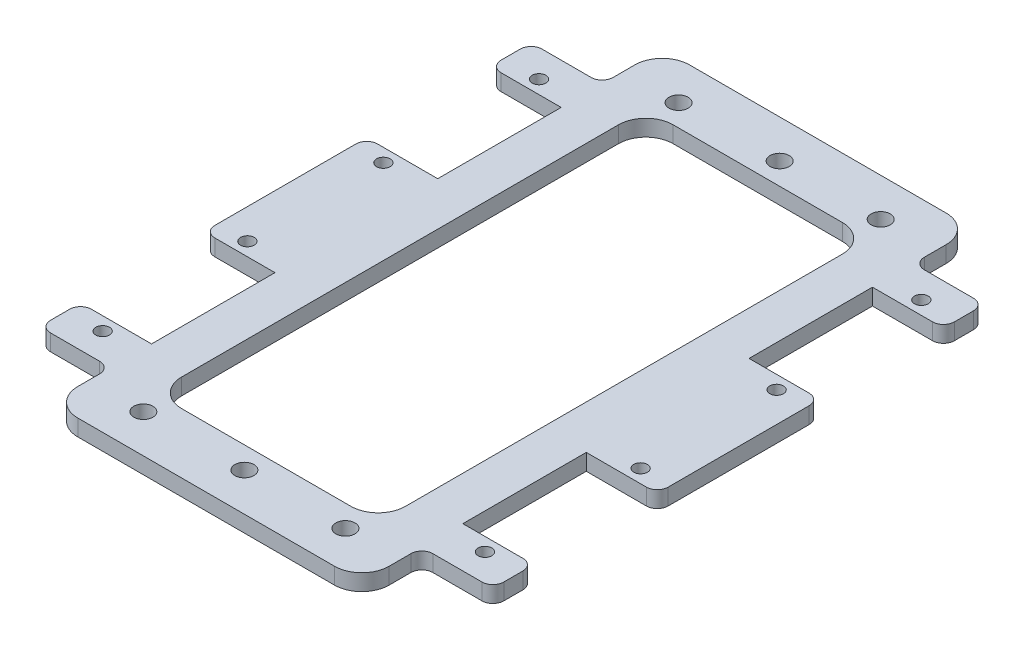
SolidWorks part; units mm, degrees
ref_plane "前视基准面" through (0, 0, 0) normal (0, 0, 1) x (1, 0, 0)
ref_plane "上视基准面" through (0, 0, 0) normal (0, 1, 0) x (1, 0, 0)
ref_plane "右视基准面" through (0, 0, 0) normal (1, 0, 0) x (0, 0, -1)
sketch "草图1" plane through (0, 0, 0) normal (0, 1, 0) x (1, 0, 0)
  line L0 (-41.5, -37.5) -> (-28.5, -37.5)
  line L1 (-28.5, -45) -> (28.5, -45)
  line L2 (-28.5, -45) -> (-28.5, 45)
  line L3 (-28.5, 45) -> (28.5, 45)
  line L4 (28.5, -45) -> (28.5, 45)
  line L5 (-28.5, -45) -> (28.5, 45) construction
  line L6 (-28.5, 45) -> (28.5, -45) construction
  line L7 (-28.5, -45) -> (28.5, -45)
  line L8 (-28.5, -45) -> (-28.5, -56)
  line L9 (-28.5, -56) -> (28.5, -56)
  line L10 (28.5, -45) -> (28.5, -56)
  line L12 (-28.5, 45) -> (-28.5, -45)
  line L13 (-28.5, -45) -> (-41.5, -45)
  line L15 (-41.5, -14.9) -> (-28.5, -14.9)
  line L16 (-41.5, 37.5) -> (-41.5, 45)
  line L17 (-41.5, 37.5) -> (-28.5, 37.5)
  line L18 (-41.5, 14.9) -> (-41.5, -14.9)
  line L19 (-41.5, -37.5) -> (-41.5, -45)
  line L20 (-28.5, 0) -> (-41.5, 0) construction
  line L21 (-41.5, 14.9) -> (-28.5, 14.9)
  line L22 (-28.5, 45) -> (-41.5, 45)
  line L23 (0, 0) -> (0, -45) construction
  line L24 (28.5, 0) -> (41.5, 0) construction
  line L25 (28.5, 45) -> (41.5, 45)
  line L26 (41.5, 14.9) -> (28.5, 14.9)
  line L27 (41.5, -37.5) -> (41.5, -45)
  line L28 (41.5, 14.9) -> (41.5, -14.9)
  line L29 (41.5, 37.5) -> (28.5, 37.5)
  line L30 (41.5, 37.5) -> (41.5, 45)
  line L31 (41.5, -14.9) -> (28.5, -14.9)
  line L32 (28.5, -45) -> (41.5, -45)
  line L33 (41.5, -37.5) -> (28.5, -37.5)
  line L34 (28.5, 45) -> (28.5, 56)
  line L35 (-28.5, 45) -> (-28.5, 56)
  line L36 (-28.5, 56) -> (28.5, 56)
  line L37 (0, -45) -> (0, -53) construction
  line L38 (-20.5, -45) -> (20.5, -45)
  line L39 (-20.5, -45) -> (-20.5, 45)
  line L40 (-20.5, 45) -> (20.5, 45)
  line L41 (20.5, -45) -> (20.5, 45)
  line L42 (-20.5, -45) -> (20.5, 45) construction
  line L43 (-20.5, 45) -> (20.5, -45) construction
  line L44 (0, -53) -> (-4, -53)
  line L45 (0, -53) -> (4, -53)
  line L46 (-4, -53) -> (-4, -45)
  line L47 (4, -53) -> (4, -45)
  line L48 (-4, -45) -> (4, -53) construction
  line L49 (-28.5, -56) -> (-21.871, -56)
  circle A0 centre (-35, -39.95) radius 1.25
  circle A1 centre (-36, -12.45) radius 1.25
  circle A2 centre (-35, 39.95) radius 1.25
  circle A3 centre (-36, 12.45) radius 1.25
  circle A4 centre (36, 12.45) radius 1.25
  circle A5 centre (35, 39.95) radius 1.25
  circle A6 centre (36, -12.45) radius 1.25
  circle A7 centre (35, -39.95) radius 1.25
  circle A8 centre (0, -49) radius 1.75
  circle A9 centre (0, 49) radius 1.75
  circle A10 centre (18.5, -49) radius 1.75
  circle A11 centre (-18.5, -49) radius 1.75
  circle A12 centre (18.5, 49) radius 1.75
  circle A13 centre (-18.5, 49) radius 1.75
  point P0 (0, 0)
  dimension "D9" = 2.5
  dimension "D10" = 2.5
  dimension "D19" = 3.5
  dimension "D1" = 90
  dimension "D2" = 57
  dimension "D3" = 11
  dimension "D4" = 13
  dimension "D5" = 7.5
  dimension "D6" = 22.6
  dimension "D7" = 29.8
  dimension "D8" = 0
  dimension "D11" = 2.45
  dimension "D12" = 2.45
  dimension "D13" = 6.5
  dimension "D14" = 7.5
  dimension "D15" = 8
  dimension "D16" = 8
  dimension "D17" = 4
  dimension "D18" = 4
  dimension "D20" = 2
  dimension "D21" = 2
extrude "凸台-拉伸1" add sketch "草图1" along normal blind 3 contours L2 L22 L16 L17 A2 | L36 L35 L3 L34 | L1 L39 L3 L2 L12 | L41 L1 L4 L3 | L29 L30 L25 L4 A5 | L31 L28 L26 L4 A4 A6 | L21 L18 L15 L12 A1 A3 | L0 L19 L13 L2 A0 | L27 L33 L4 L32 A7 | L10 L1 L7 L8 L9 | L45 L47 L38 L46 L44 A8
fillet "圆角1" radius 2 12 edges at (41.5, 1.5, -45) (41.5, 1.5, -37.5) (41.5, 1.5, -14.9) (41.5, 1.5, 14.9) (41.5, 1.5, 37.5) (41.5, 1.5, 45) (-41.5, 1.5, 45) (-41.5, 1.5, 37.5) (-41.5, 1.5, -14.9) (-41.5, 1.5, -45) (-41.5, 1.5, -37.5) (-41.5, 1.5, 14.9)
fillet "圆角2" radius 5 8 edges at (20.5, 1.5, 45) (-20.5, 1.5, 45) (-20.5, 1.5, -45) (20.5, 1.5, -45) (-28.5, 1.5, -56) (28.5, 1.5, -56) (28.5, 1.5, 56) (-28.5, 1.5, 56)
fillet "圆角3" radius 2 4 edges at (28.5, 1.5, -45) (-28.5, 1.5, -45) (-28.5, 1.5, 45) (28.5, 1.5, 45)
